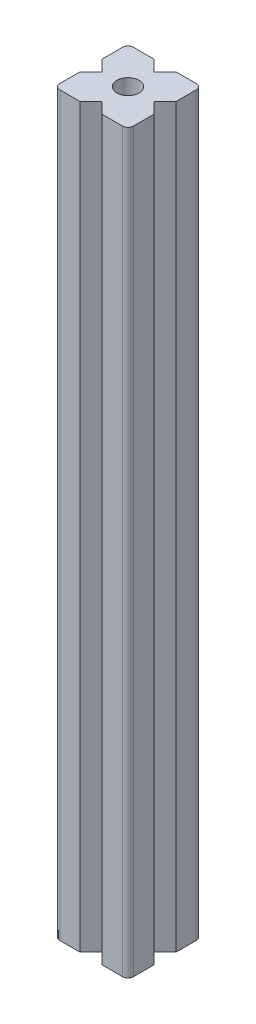
SolidWorks part; units mm, degrees
ref_plane "Front" through (0, 0, 0) normal (0, 0, 1) x (1, 0, 0)
ref_plane "Top" through (0, 0, 0) normal (0, 1, 0) x (1, 0, 0)
ref_plane "Right" through (0, 0, 0) normal (1, 0, 0) x (0, 0, -1)
sketch "Skizze1" plane through (0, 0, 0) normal (0, 1, 0) x (1, 0, 0)
  line L1 (0, 0) -> (20, 0)
  line L2 (0, 0) -> (0, 20)
  line L3 (0, 20) -> (20, 20)
  line L4 (20, 0) -> (20, 20)
  dimension "D1" = 20
extrude "Aufsatz-Linear austragen1" add sketch "Skizze1" along normal blind 200
sketch "Skizze2" plane through (0, 200, 0) normal (0, 1, 0) x (1, 0, 0)
  line L0 (10, 20) -> (10, 0) construction
  line L1 (0, 10) -> (20, 10) construction
  line L2 (7, 20) -> (10, 17)
  line L3 (13, 20) -> (10, 17)
  line L4 (10, 10) -> (20, 20) construction
  line L5 (7, 20) -> (13, 20)
  line L6 (20, 13) -> (17, 10)
  line L7 (20, 7) -> (17, 10)
  line L8 (20, 7) -> (20, 13)
  line L9 (0, 7) -> (0, 13)
  line L10 (0, 7) -> (3, 10)
  line L11 (0, 13) -> (3, 10)
  line L12 (7, 0) -> (13, 0)
  line L13 (13, 0) -> (10, 3)
  line L14 (7, 0) -> (10, 3)
  line L15 (20, 20) -> (0, 20) construction
  line L16 (20, 0) -> (20, 20) construction
  line L17 (0, 0) -> (20, 0) construction
  dimension "D1" = 3
  dimension "D2" = 3
extrude "Schnitt-Linear austragen1" cut sketch "Skizze2" against normal through all
ref_plane "Ebene1" through (10, 0, 0) normal (1, 0, 0) x (0, 0, -1)
sketch "Skizze3" plane through (0, 200, 0) normal (0, 1, 0) x (1, 0, 0)
  line L0 (3, 10) -> (17, 10) construction
  circle A0 centre (10, 10) radius 3
  dimension "D1" = 6
extrude "Schnitt-Linear austragen2" cut sketch "Skizze3" against normal through all
ref_plane "Plane1" through (0, 100, 0) normal (0, 1, 0) x (1, 0, 0)
ref_plane "Plane2" through (0, 0, -10) normal (0, 0, -1) x (-1, 0, 0)
fillet "Fillet1" radius 1.5 4 edges at (20, 100, 0) (20, 100, -20) (0, 100, -20) (0, 100, 0)
